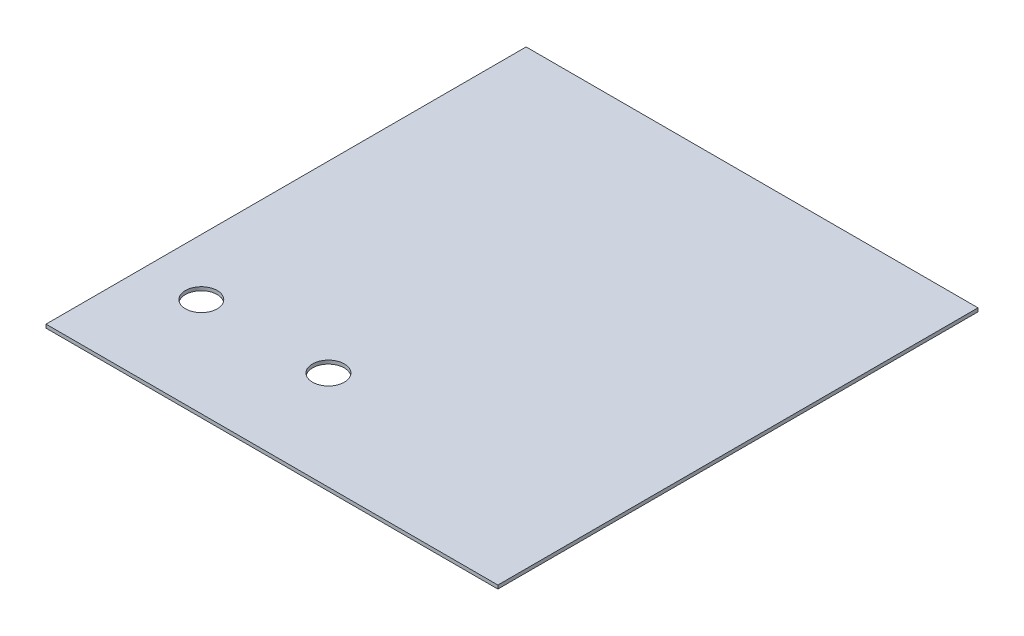
SolidWorks part; units mm, degrees
ref_plane "Front Plane" through (0, 0, 0) normal (0, 0, 1) x (1, 0, 0)
ref_plane "Top Plane" through (0, 0, 0) normal (0, 1, 0) x (1, 0, 0)
ref_plane "Right Plane" through (0, 0, 0) normal (1, 0, 0) x (0, 0, -1)
sketch "Sketch1" plane through (0, 0, 0) normal (0, 1, 0) x (1, 0, 0)
  line L1 (0, 0) -> (406.4, 0)
  line L2 (0, 0) -> (0, 431.8)
  line L3 (0, 431.8) -> (406.4, 431.8)
  line L4 (406.4, 0) -> (406.4, 431.8)
  dimension "D1" = 406.4
  dimension "D2" = 431.8
extrude "Boss-Extrude1" add sketch "Sketch1" along normal blind 3.175
sketch "Sketch2" plane through (0, 3.175, 0) normal (0, 1, 0) x (1, 0, 0)
  line L0 (0, 431.8) -> (0, 0) construction
  line L3 (50.8, 88.9) -> (165.1, 88.9) construction
  line L4 (0, 0) -> (406.4, 0) construction
  circle A2 centre (50.8, 88.9) radius 14.2875
  circle A3 centre (165.1, 88.9) radius 14.2875
  dimension "D1" = 50.8
  dimension "D3" = 28.575
  dimension "D4" = 28.575
  dimension "D5" = 114.3
  dimension "D8" = 88.9
extrude "Cut-Extrude1" cut sketch "Sketch2" against normal blind 3.175
